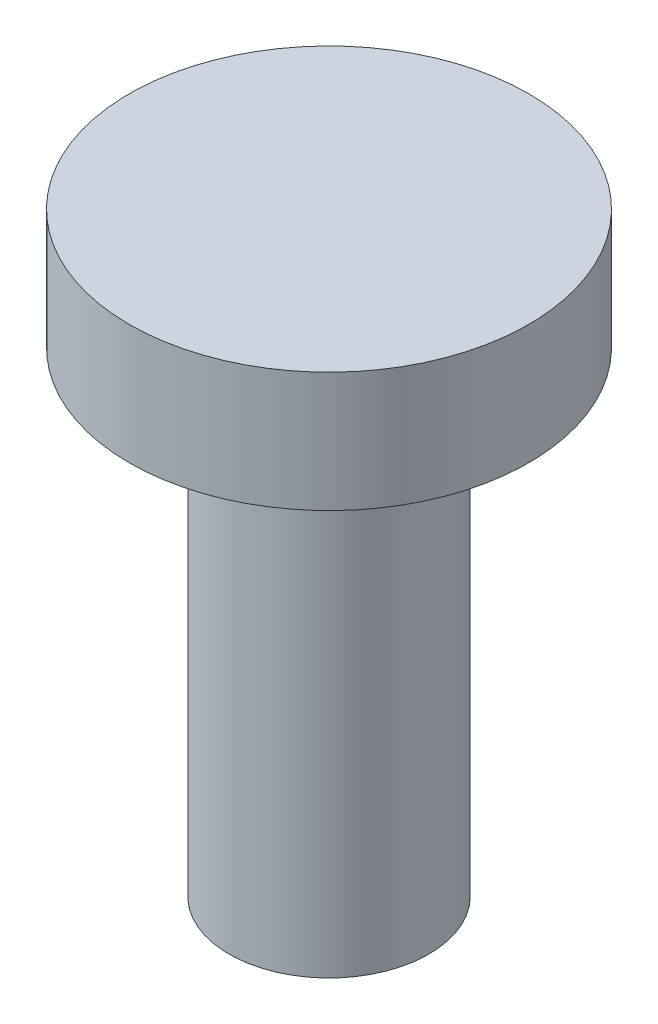
SolidWorks part; units mm, degrees
ref_plane "Front Plane" through (0, 0, 0) normal (0, 0, 1) x (1, 0, 0)
ref_plane "Top Plane" through (0, 0, 0) normal (0, 1, 0) x (1, 0, 0)
ref_plane "Right Plane" through (0, 0, 0) normal (1, 0, 0) x (0, 0, -1)
sketch "Sketch1" plane through (0, 0, 0) normal (0, 1, 0) x (1, 0, 0)
  circle A0 centre (0, 0) radius 5
  dimension "D1" = 10
extrude "Boss-Extrude1" add sketch "Sketch1" along normal blind 3
sketch "Sketch2" plane through (0, 0, 0) normal (0, -1, 0) x (1, 0, 0)
  circle A0 centre (0, 0) radius 2.5
  dimension "D1" = 5
extrude "Boss-Extrude2" add sketch "Sketch2" along normal blind 11.8999
